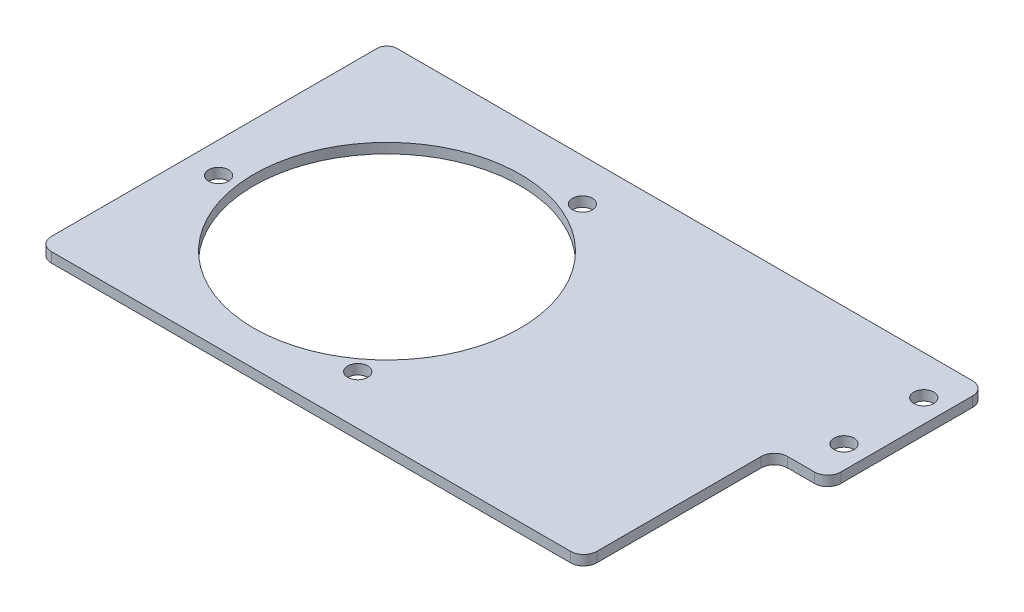
SolidWorks part; units mm, degrees
ref_plane "Front Plane" through (0, 0, 0) normal (0, 0, 1) x (1, 0, 0)
ref_plane "Top Plane" through (0, 0, 0) normal (0, 1, 0) x (1, 0, 0)
ref_plane "Right Plane" through (0, 0, 0) normal (1, 0, 0) x (0, 0, -1)
sketch "Sketch5" plane through (0, 0, 0) normal (0, 1, 0) x (1, 0, 0)
  line L0 (-108.5113, 114.8574) -> (257.5911, 114.8574)
  line L1 (265.9438, 106.5046) -> (265.9438, 22.6846)
  line L2 (257.5911, 14.3319) -> (240.397, 14.3319)
  line L3 (232.0442, 5.9791) -> (232.0442, -98.5839)
  line L4 (223.6915, -106.9367) -> (-106.5085, -106.9367)
  line L5 (-114.8613, -98.5839) -> (-114.8613, 108.5074)
  line L6 (265.9438, 64.5946) -> (253.9936, 64.5946) construction
  arc A0 (-108.5113, 114.8574) -> (-114.8613, 108.5074) centre (-108.5113, 108.5074) ccw
  arc A1 (-106.5085, -106.9367) -> (-114.8613, -98.5839) centre (-106.5085, -98.5839) cw
  arc A2 (232.0442, -98.5839) -> (223.6915, -106.9367) centre (223.6915, -98.5839) cw
  arc A3 (240.397, 14.3319) -> (232.0442, 5.9791) centre (240.397, 5.9791) ccw
  arc A4 (265.9438, 22.6846) -> (257.5911, 14.3319) centre (257.5911, 22.6846) cw
  arc A5 (257.5911, 114.8574) -> (265.9438, 106.5046) centre (257.5911, 106.5046) cw
  circle A6 centre (0, 0) radius 84.7725
  circle A7 centre (251.46, 89.9682) radius 6.35
  circle A8 centre (251.46, 39.2211) radius 6.35
  circle A9 centre (-95.2384, -11.8444) radius 6.35
  circle A12 centre (57.0353, -75.6468) radius 6.35
  circle A14 centre (36.1529, 88.1273) radius 6.35
  point P37 (0, 0)
  dimension "D1" = 6.35
  dimension "D2" = 169.545
  dimension "D3" = 207.0913
  dimension "D4" = 366.1024
  dimension "D5" = 83.82
  dimension "D6" = 330.2
  dimension "D7" = 104.563
extrude "Boss-Extrude1" add sketch "Sketch5" against normal blind 6.35
